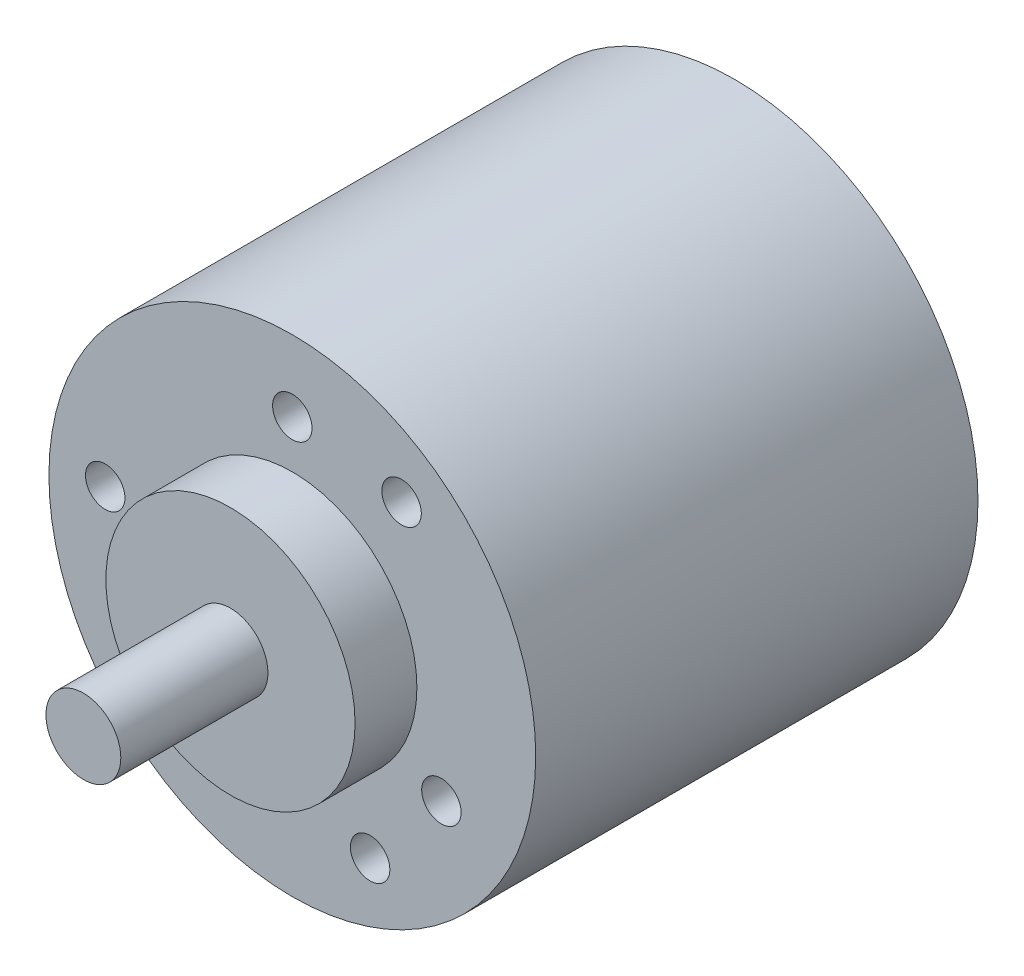
SolidWorks part; units mm, degrees
material "6061-T6 (SS)"
ref_plane "Front Plane" through (0, 0, 0) normal (0, 0, 1) x (1, 0, 0)
ref_plane "Top Plane" through (0, 0, 0) normal (0, 1, 0) x (1, 0, 0)
ref_plane "Right Plane" through (0, 0, 0) normal (1, 0, 0) x (0, 0, -1)
sketch "Sketch1" plane through (0, 0, 0) normal (0, 0, 1) x (1, 0, 0)
  circle A0 centre (0, 0) radius 19.5
extrude "Boss-Extrude1" add sketch "Sketch1" against normal blind 35.433
sketch "Sketch2" plane through (0, 0, 0) normal (0, 0, 1) x (1, 0, 0)
  circle A0 centre (0, 0) radius 9.9822
extrude "Boss-Extrude2" add sketch "Sketch2" along normal blind 4.953
sketch "Sketch4" plane through (0, 0, 4.953) normal (0, 0, 1) x (1, 0, 0)
  circle A0 centre (0, 0) radius 3
extrude "Boss-Extrude3" add sketch "Sketch4" along normal blind 11.7856
sketch "Sketch5" plane through (0, 0, 0) normal (0, 0, 1) x (1, 0, 0)
  line L1 (0, 13.7922) -> (-11.9444, -6.8961) construction
  line L2 (-11.9444, -6.8961) -> (11.9444, -6.8961) construction
  line L3 (11.9444, -6.8961) -> (0, 13.7922) construction
  line L4 (8.7558, 12.2532) -> (-14.9894, 1.4561) construction
  line L5 (-14.9894, 1.4561) -> (6.2337, -13.7093) construction
  line L6 (6.2337, -13.7093) -> (8.7558, 12.2532) construction
  circle A0 centre (0, 0) radius 6.8961 construction
  circle A1 centre (0, 0) radius 13.7922 construction
  circle A2 centre (-11.9444, -6.8961) radius 1.58
  circle A3 centre (11.9444, -6.8961) radius 1.58
  circle A5 centre (0, 13.7922) radius 1.58
  circle A6 centre (0, 0) radius 15.06 construction
  circle A7 centre (0, 0) radius 7.53 construction
  circle A8 centre (8.7558, 12.2532) radius 1.58
  circle A9 centre (6.2337, -13.7093) radius 1.58
  circle A10 centre (-14.9894, 1.4561) radius 1.58
  dimension "D3" = 13.7922
  dimension "D2" = 8.89
extrude "Cut-Extrude1" cut sketch "Sketch5" against normal blind 5.08
